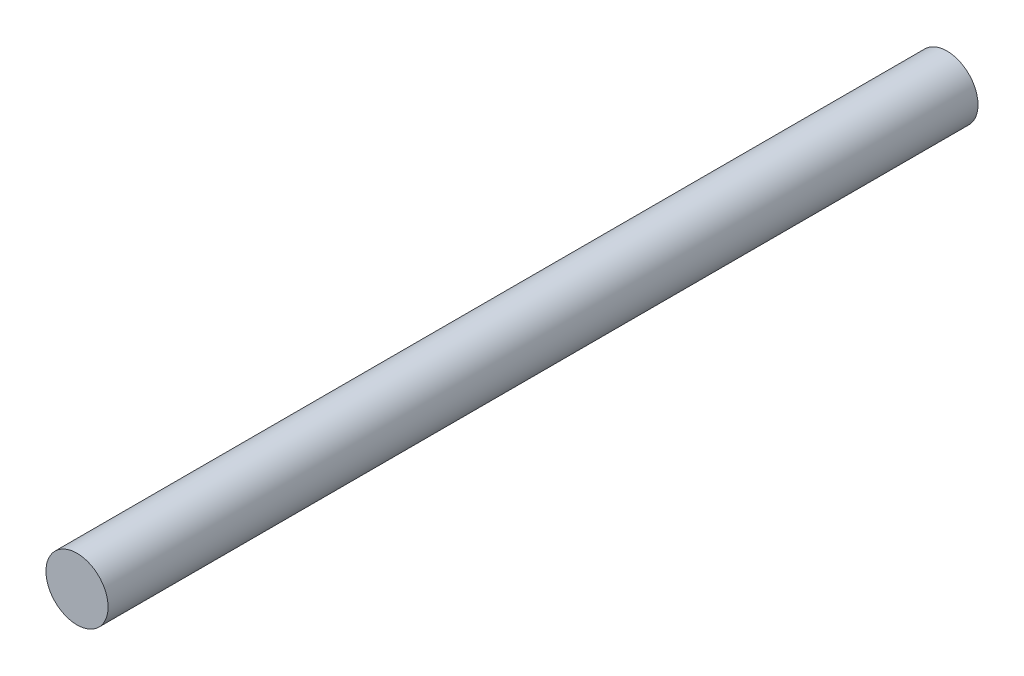
SolidWorks part; units mm, degrees
ref_plane "Front" through (0, 0, 0) normal (0, 0, 1) x (1, 0, 0)
ref_plane "Top" through (0, 0, 0) normal (0, 1, 0) x (1, 0, 0)
ref_plane "Right" through (0, 0, 0) normal (1, 0, 0) x (0, 0, -1)
sketch "Sketch1" plane through (0, 0, 0) normal (0, 0, 1) x (1, 0, 0)
  circle A0 centre (0, 0) radius 6.35
  dimension "D1" = 12.7
extrude "Extrude1" add sketch "Sketch1" along normal blind 88.9 and the other way blind 88.9
